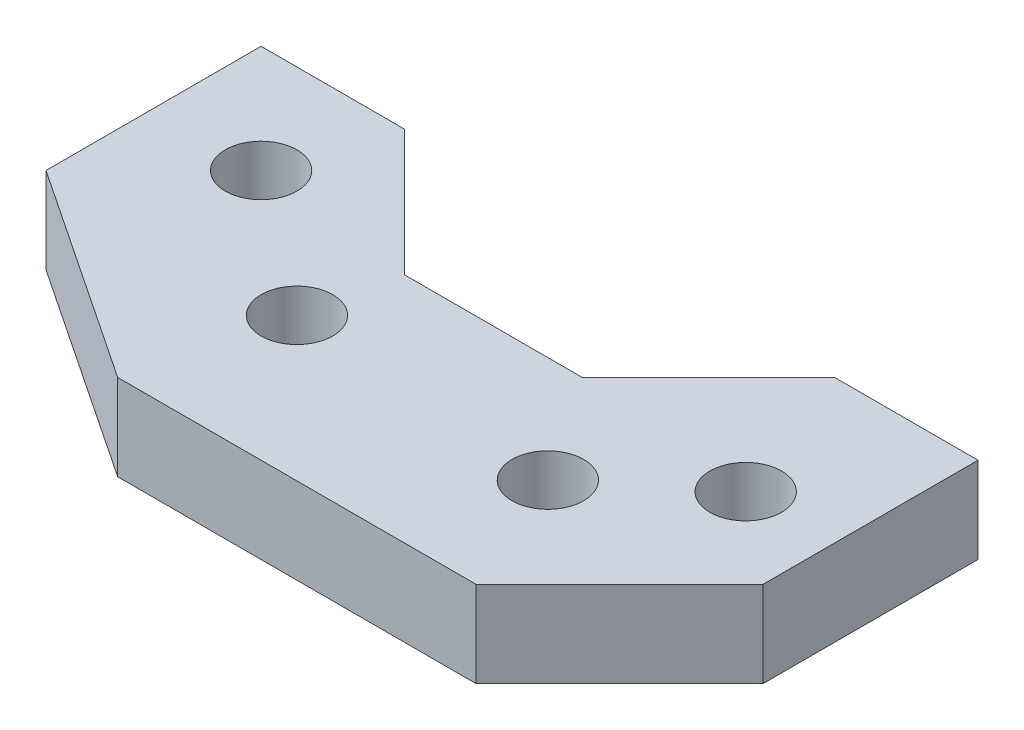
SolidWorks part; units mm, degrees
ref_plane "Front Plane" through (0, 0, 0) normal (0, 0, 1) x (1, 0, 0)
ref_plane "Top Plane" through (0, 0, 0) normal (0, 1, 0) x (1, 0, 0)
ref_plane "Right Plane" through (0, 0, 0) normal (1, 0, 0) x (0, 0, -1)
sketch "Sketch1" plane through (0, 0, 0) normal (0, 1, 0) x (1, 0, 0)
  line L0 (0, 0) -> (0, -38.1)
  line L1 (0, -38.1) -> (38.1, -63.5)
  line L2 (38.1, -63.5) -> (101.6, -63.5)
  line L3 (101.6, -63.5) -> (127, -38.1)
  line L4 (127, -38.1) -> (127, 0)
  line L5 (127, 0) -> (101.6, 0)
  line L8 (47.752, -22.352) -> (25.4, 0)
  line L9 (25.4, 0) -> (0, 0)
  line L10 (101.6, 0) -> (79.248, -22.352)
  line L11 (47.752, -22.352) -> (79.248, -22.352)
  circle A0 centre (19.05, -19.05) radius 6.35
  circle A1 centre (44.45, -38.1) radius 6.35
  circle A2 centre (91.948, -41.148) radius 6.35
  circle A3 centre (111.252, -25.4) radius 6.35
  dimension "D12" = 12.7
  dimension "D2" = 25.4
  dimension "D3" = 38.1
  dimension "D4" = 25.4
  dimension "D5" = 25.4
  dimension "D6" = 47.752
  dimension "D7" = 127
  dimension "D8" = 63.5
  dimension "D9" = 63.5
  dimension "D10" = 45
  dimension "D11" = 63.5
  dimension "D13" = 22.352
  dimension "D14" = 47.752
  dimension "D15" = 19.05
  dimension "D16" = 19.05
  dimension "D17" = 44.45
  dimension "D18" = 25.4
  dimension "D19" = 47.498
  dimension "D20" = 22.352
  dimension "D21" = 15.748
  dimension "D22" = 25.4
extrude "Boss-Extrude1" add sketch "Sketch1" along normal blind 15.24
